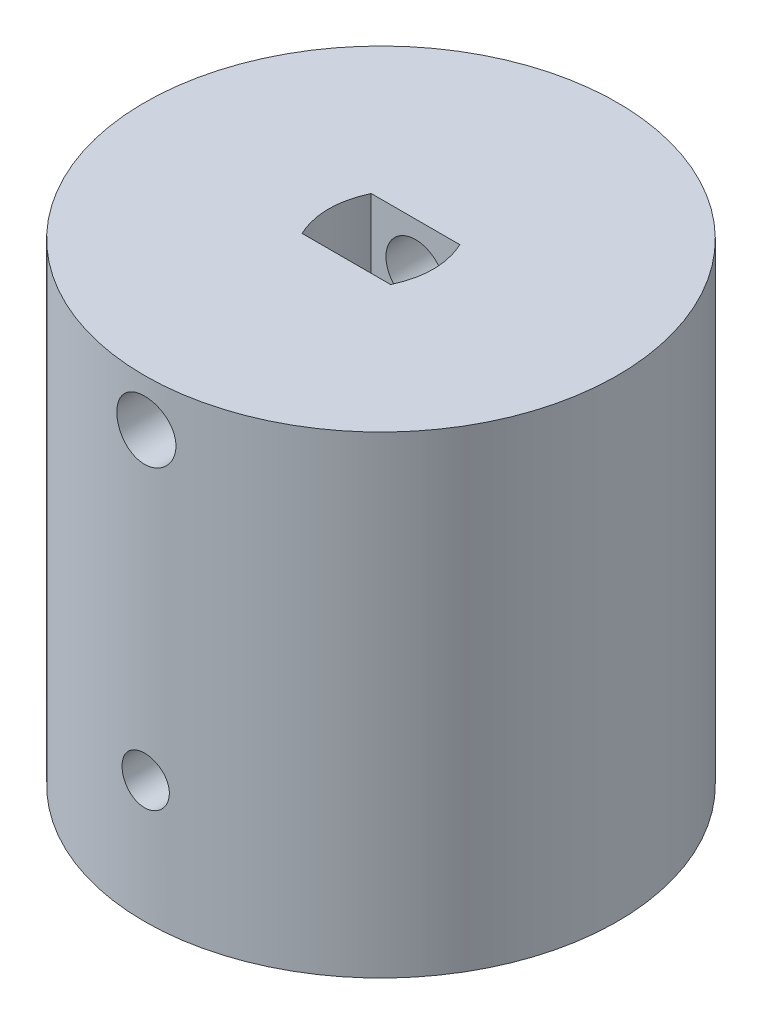
SolidWorks part; units mm, degrees
ref_plane "Front Plane" through (0, 0, 0) normal (0, 0, 1) x (1, 0, 0)
ref_plane "Top Plane" through (0, 0, 0) normal (0, 1, 0) x (1, 0, 0)
ref_plane "Right Plane" through (0, 0, 0) normal (1, 0, 0) x (0, 0, -1)
sketch "Sketch1" plane through (0, 0, 0) normal (0, 1, 0) x (1, 0, 0)
  circle A0 centre (0, 0) radius 20
  dimension "D1" = 40
extrude "Boss-Extrude1" add sketch "Sketch1" along normal blind 40
sketch "Sketch2" plane through (0, 0, 0) normal (0, -1, 0) x (1, 0, 0)
  line L0 (-4, 5) -> (4, 5)
  line L1 (-4, -5) -> (4, -5)
  spline S0 degree 2 poles (-4, 5) (-8.2, -0.0056) (-4, -5) knots 0 0 0 1 1 1
  spline S1 degree 2 poles (4, 5) (8.2, 0.0092) (4, -5) knots 0 0 0 1 1 1
  dimension "D2" = 0
  dimension "D1" = 10
  dimension "D3" = 5
  dimension "D4" = 12.2
  dimension "D5" = 8
  dimension "D6" = 6.1
extrude "Cut-Extrude1" cut sketch "Sketch2" against normal blind 15
sketch "Sketch3" plane through (0, 0, -5) normal (0, 0, 1) x (1, 0, 0)
  circle A0 centre (0, 12.0042) radius 2
  dimension "D1" = 4
extrude "Cut-Extrude2" cut sketch "Sketch3" against normal blind 15
sketch "Sketch4" plane through (0, 40, 0) normal (0, 1, 0) x (1, 0, 0)
  line L0 (-3.75, 2.925) -> (3.75, 2.925)
  line L1 (-3.75, -2.925) -> (3.75, -2.925)
  spline S0 degree 2 poles (-3.75, 2.925) (-5.1, 0) (-3.75, -2.925) knots 0 0 0 1 1 1
  spline S1 degree 2 poles (3.75, 2.925) (5.1, 0) (3.75, -2.925) knots 0 0 0 1 1 1
  point P5 (-6.2688, 0)
  point P8 (4.3178, 0)
  point P9 (-4.3939, 0)
  point P10 (3.1826, 3.272)
  point P11 (4.0565, 0)
  point P12 (-5.6289, 0)
  point P13 (-5.4832, 0)
  point P14 (-3.335, -0.3691)
  point P16 (-4.425, 0)
  dimension "D6" = 3.75
  dimension "D1" = 8.85
  dimension "D2" = 0
  dimension "D3" = 5.85
  dimension "D4" = 2.925
  dimension "D5" = 7.5
extrude "Cut-Extrude3" cut sketch "Sketch4" against normal blind 9
sketch "Sketch5" plane through (0, 0, 2.925) normal (0, 0, -1) x (-1, 0, 0)
  circle A0 centre (0, 36) radius 2.5
  dimension "D2" = 5
extrude "Cut-Extrude4" cut sketch "Sketch5" against normal through all both and the other way through all
sketch "Sketch6" plane through (0, 0, 0) normal (0, -1, 0) x (1, 0, 0)
  line L0 (-5.21, 14.68) -> (-5.21, 8.5)
  line L1 (-5.21, 14.68) -> (5.21, 14.68)
  line L2 (5.21, 14.68) -> (5.21, 8.5)
  line L3 (5.21, 8.5) -> (-5.21, 8.5)
  line L4 (4, 5) -> (-4, 5) construction
  dimension "D1" = 10.42
  dimension "D2" = 6.18
  dimension "D3" = 5.21
  dimension "D4" = 3.5
extrude "Cut-Extrude5" cut sketch "Sketch6" against normal blind 15
sketch "Sketch7" plane through (0, 0, 8.5) normal (0, 0, 1) x (1, 0, 0)
  circle A0 centre (0, 10.34) radius 2
  dimension "D3" = 4
extrude "Cut-Extrude6" cut sketch "Sketch7" against normal blind 10 and the other way blind 15
